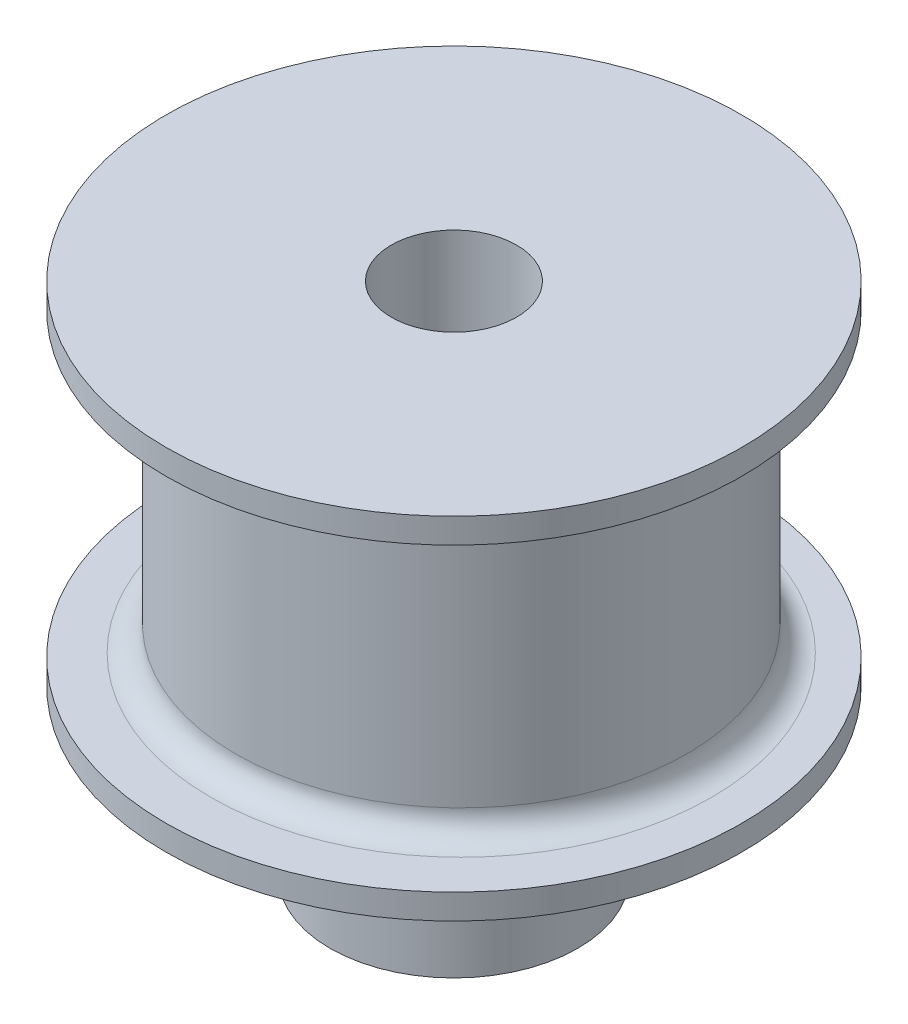
SolidWorks part; units mm, degrees
ref_plane "Front Plane" through (0, 0, 0) normal (0, 0, 1) x (1, 0, 0)
ref_plane "Top Plane" through (0, 0, 0) normal (0, 1, 0) x (1, 0, 0)
ref_plane "Right Plane" through (0, 0, 0) normal (1, 0, 0) x (0, 0, -1)
sketch "Sketch1" plane through (0, 0, 0) normal (0, 1, 0) x (1, 0, 0)
  circle A0 centre (0, 0) radius 4.95
extrude "Boss-Extrude2" add sketch "Sketch1" along normal blind 6.6 contours A0
sketch "Sketch4" plane through (0, 6.6, 0) normal (0, 1, 0) x (1, 0, 0)
  circle A0 centre (0, 0) radius 11.5
extrude "Boss-Extrude3" add sketch "Sketch4" along normal blind 1
sketch "Sketch5" plane through (0, 7.6, 0) normal (0, 1, 0) x (1, 0, 0)
  circle A0 centre (0, 0.2911) radius 9
extrude "Boss-Extrude4" add sketch "Sketch5" along normal blind 12
sketch "Sketch6" plane through (0, 19.6, 0) normal (0, 1, 0) x (1, 0, 0)
  circle A0 centre (0, 0) radius 11.5
extrude "Boss-Extrude5" add sketch "Sketch6" along normal blind 1
fillet "Fillet1" radius 1 1 edges at (0, 7.6, 8.7089)
fillet "Fillet2" radius 1 1 edges at (0, 19.6, 8.7089)
sketch "Sketch7" plane through (0, 0, 0) normal (0, -1, 0) x (1, 0, 0)
  circle A0 centre (0, 0) radius 2.5
extrude "Cut-Extrude1" cut sketch "Sketch7" against normal through all
